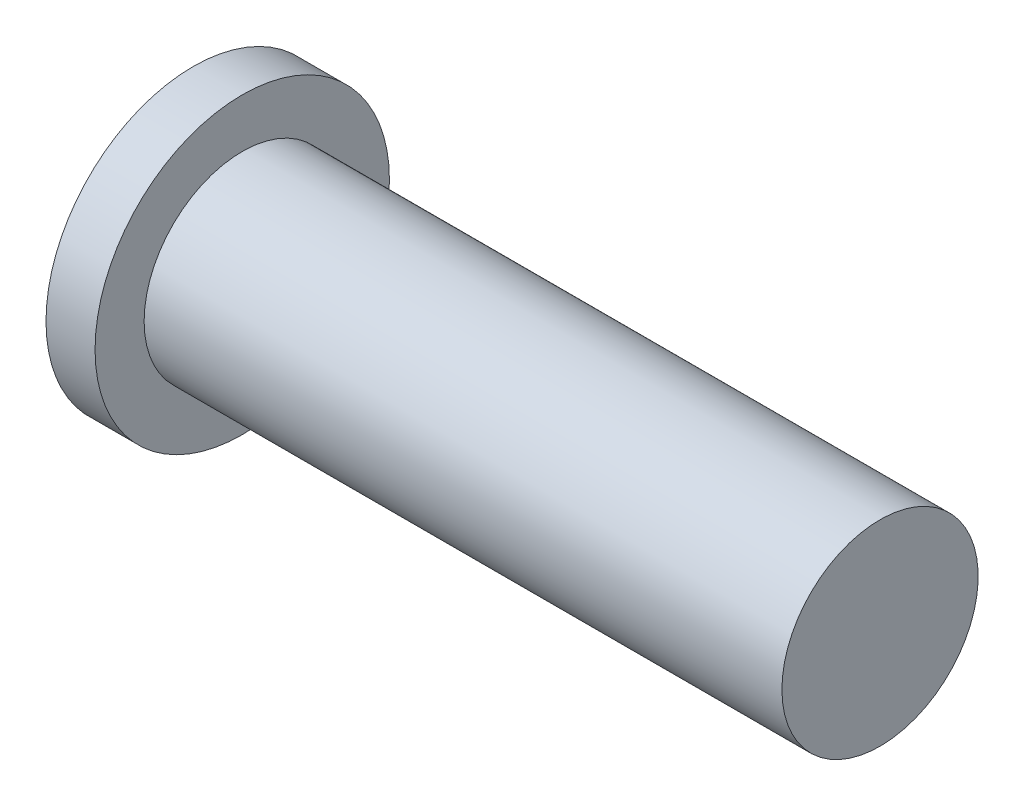
SolidWorks part; units mm, degrees
ref_plane "Plane1" through (0, 0, 0) normal (0, 0, 1) x (1, 0, 0)
ref_plane "Plane2" through (0, 0, 0) normal (0, 1, 0) x (1, 0, 0)
ref_plane "Plane3" through (0, 0, 0) normal (1, 0, 0) x (0, 0, -1)
sketch "BodySke" plane through (0, 0, 0) normal (0, 0, 1) x (1, 0, 0)
  line L0 (3.1, 2) -> (3.1, 3)
  line L1 (3.1, 3) -> (2.1, 3)
  line L2 (-25.4, 0) -> (127, 0) construction
  line L3 (16.1, 0) -> (2.1, 0)
  line L4 (3.1, 2) -> (16.1, 2)
  line L5 (16.1, 2) -> (16.1, 0)
  line L7 (3.1, -2) -> (16.1, -2) construction
  line L8 (0, -4) -> (3.1, -4) construction
  line L9 (3.8, 3.5875) -> (3.8, -5.9375) construction
  line L10 (3.1, 6.35) -> (3.1, -3.175) construction
  line L11 (2.1, 3) -> (2.1, 0)
  point P15 (0, 4)
  dimension "Diameter" = 4
  dimension "Length" = 13
  dimension "Advance" = 0.7
  dimension "Thread_nom" = 13
revolve "Base-Revolve" add sketch "BodySke" angle 360 about L2
cosmetic thread "ThreadCosmetic" [suppressed] parameters "Thread_length"=12.3, "Thread_minor"=3.22
sketch "ThdSchSke" plane through (0, 0, 0) normal (0, 0, 1) x (1, 0, 0)
  line L0 (3.8, -1.61) -> (3.5269, -2)
  line L1 (3.8, -1.61) -> (4.0731, -2)
  line L2 (4.0731, -2) -> (4.0731, -2.5)
  line L3 (-3.175, 0) -> (5.1513, 0) construction
  line L5 (4.0731, -2.5) -> (3.5269, -2.5)
  line L6 (3.5269, -2.5) -> (3.5269, -2)
  dimension "Thread_minor" = 3.22
  dimension "Diameter" = 4
  dimension "Start" = 3.8
  dimension "SideAngle" = 55
  dimension "VeeAngle" = 70
  dimension "Overcut" = 5
revolve "ThreadSchematic" [suppressed] cut sketch "ThdSchSke" angle 360 about L3
pattern_linear "ThdSchPat" [suppressed]
